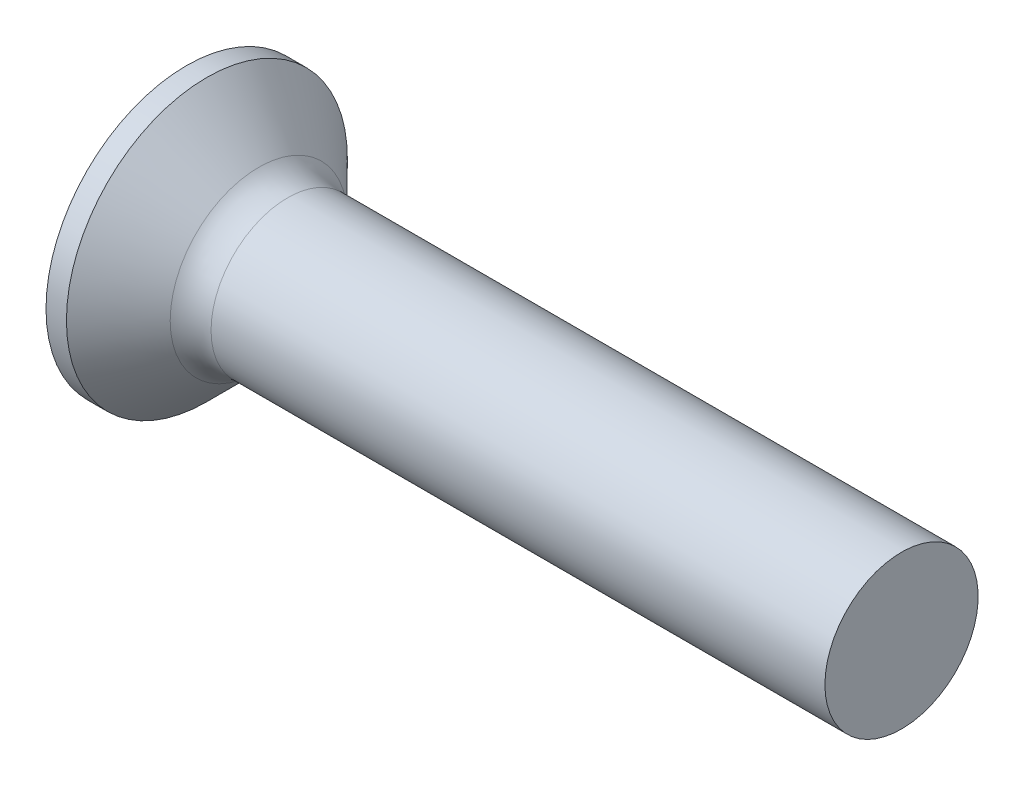
SolidWorks part; units mm, degrees
revolve "Base-Revolve" add sketch "BodySke"
sketch "BodySke" plane through (0, 0, 0) normal (0, 0, 1) x (1, 0, 0)
  line L0 (0, 0) -> (0, 2.75)
  line L1 (0, 2.75) -> (0.4, 2.75)
  line L2 (1.65, 1.5) -> (14, 1.5)
  line L3 (14, 1.5) -> (14, 0)
  line L4 (14, 0) -> (0, 0)
  line L5 (-6.35, 0) -> (82.55, 0) construction
  line L6 (1.65, -1.5) -> (14, -1.5) construction
  line L7 (0.4, -2.75) -> (1.65, -1.5) construction
  line L8 (0.4, 2.75) -> (1.65, 1.5)
  line L9 (0, -2.75) -> (0.4, -2.75) construction
  line L10 (2.15, 3.0875) -> (2.15, -6.4375) construction
  line L11 (2, 6.35) -> (2, -3.175) construction
  dimension "Diameter" = 3
  dimension "Length" = 14
  dimension "Head_ht" = 1.65
  dimension "Head_dia" = 5.5
  dimension "Head_ang" = 90
  dimension "D6" = 0.4
  dimension "Advance" = 0.5
  dimension "Thread_nom" = 12
cosmetic thread "ThreadCosmetic" [suppressed]
fillet "Fillet1" radius 0.8 1 edges at (1.65, 0, 1.5)
ref_plane "Plane1" through (0, 0, 0) normal (0, 0, 1) x (1, 0, 0)
ref_plane "Plane2" through (0, 0, 0) normal (0, 1, 0) x (1, 0, 0)
ref_plane "Plane3" through (0, 0, 0) normal (1, 0, 0) x (0, 0, -1)
sketch "Sketch3" plane through (0, 0, 0) normal (-1, 0, 0) x (0, 0, 1)
  line L0 (-0.37, 1.5) -> (0.37, 1.5)
  line L1 (0.37, 1.5) -> (0.37, -1.5)
  line L2 (0.37, -1.5) -> (-0.37, -1.5)
  line L3 (-0.37, -1.5) -> (-0.37, 1.5)
  dimension "Cross_dia" = 3
  dimension "Cross_width" = 0.74
  dimension "D1" = 1.5
  dimension "D2" = 0.37
ref_plane "Plane4" through (2.01, 0, 0) normal (-1, 0, 0) x (0, 0, 1)
sketch "Sketch4" plane through (2.01, 0, 0) normal (-1, 0, 0) x (0, 0, 1)
  line L0 (-0.37, 0.4979) -> (0.37, 0.4979)
  line L3 (0.37, 0.4979) -> (0.37, -0.4979)
  line L4 (0.37, -0.4979) -> (-0.37, -0.4979)
  line L5 (-0.37, -0.4979) -> (-0.37, 0.4979)
  dimension "D2" = 0.9957
  dimension "D1" = 0.74
  dimension "D4" = 0.4979
  dimension "D3" = 0.37
loft "Recess" cut profiles "Sketch3", "Sketch4"
pattern_circular "RecPat" count 2 every 90 about axis through (0, 0, 0) along (1, 0, 0) of "Recess"
sketch "RecCorSke" plane through (0, 0, 0) normal (0, 0, 1) x (1, 0, 0)
  line L0 (-3.175, 0) -> (15.875, 0) construction
  line L2 (0, 0) -> (0, 0.6966)
  line L3 (0, 0.6966) -> (2.01, 0.556)
  line L4 (2.01, 0.556) -> (2.1907, 0)
  line L5 (2.1907, 0) -> (0, 0)
  dimension "Diameter" = 1.112
  dimension "Depth" = 2.01
  dimension "Draft_angle" = 4
  dimension "Bottom_angle" = 18
revolve "RecessCore" cut sketch "RecCorSke" angle 360 about L0
sketch "ThdSchSke" plane through (0, 0, 0) normal (0, 0, 1) x (1, 0, 0)
  line L0 (2.15, -1.2195) -> (1.9536, -1.5)
  line L1 (2.15, -1.2195) -> (2.3464, -1.5)
  line L2 (2.3464, -1.5) -> (2.3464, -1.875)
  line L3 (-3.175, 0) -> (5.1513, 0) construction
  line L5 (2.3464, -1.875) -> (1.9536, -1.875)
  line L6 (1.9536, -1.875) -> (1.9536, -1.5)
  line L7 (0, 2.75) -> (0, -2.75) construction
  dimension "Diameter" = 3
  dimension "Thread_minor" = 2.439
  dimension "Start" = 2.15
revolve "ThreadSchematic" [suppressed] cut sketch "ThdSchSke" angle 360 about L3
pattern_linear "ThdSchPat" [suppressed]
equation "\"D1@Sketch3\" = \"Cross_dia@Sketch3\" / 2"
equation "\"D2@Sketch3\" = \"Cross_width@Sketch3\" / 2"
equation "\"Depth@RecCorSke\" = \"Cross_depth@Plane4\""
equation "\"D1@Sketch4\" = \"Cross_width@Sketch3\""
equation "\"D2@Sketch4\" = \"Cross_dia@Sketch3\" - 2.0 * \"Cross_depth@Plane4\" * tan(26.5  * 0.017453292)"
equation "\"D3@Sketch4\" = \"D1@Sketch4\" / 2"
equation "\"D4@Sketch4\" = \"D2@Sketch4\" / 2"
equation "\"Thread_length@ThreadCosmetic\" = ((sgn( (\"Length@BodySke\" - \"Advance@BodySke\" * 1.0 - \"Head_ht@BodySke\" ) - \"Thread_nom@BodySke\" )-1)*( (\"Length@BodySke\" - \"Advance@BodySke\" * 1.0 - \"Head_ht@BodySke\" ) - \"Thread_nom@BodySke\" ))/-2+ \"Thread_nom@BodySke\""
equation "\"Thread_minor@ThdSchSke\" = \"Thread_minor@ThreadCosmetic\""
equation "\"Diameter@ThdSchSke\" = \"Diameter@BodySke\""
equation "\"Overcut@ThdSchSke\" = \"Diameter@BodySke\" * 1.25"
equation "\"Start@ThdSchSke\" = 0.000001 + \"Length@BodySke\" - \"Thread_length@ThreadCosmetic\"  '---Countersunk---"
equation "\"Num_threads@ThdSchPat\" = int( \"Thread_length@ThreadCosmetic\" / \"Advance@BodySke\" + 0.999 )  + 1"
equation "\"Advance@ThdSchPat\" = \"Thread_length@ThreadCosmetic\" /  (\"Num_threads@ThdSchPat\" - 1) 'relax it"
